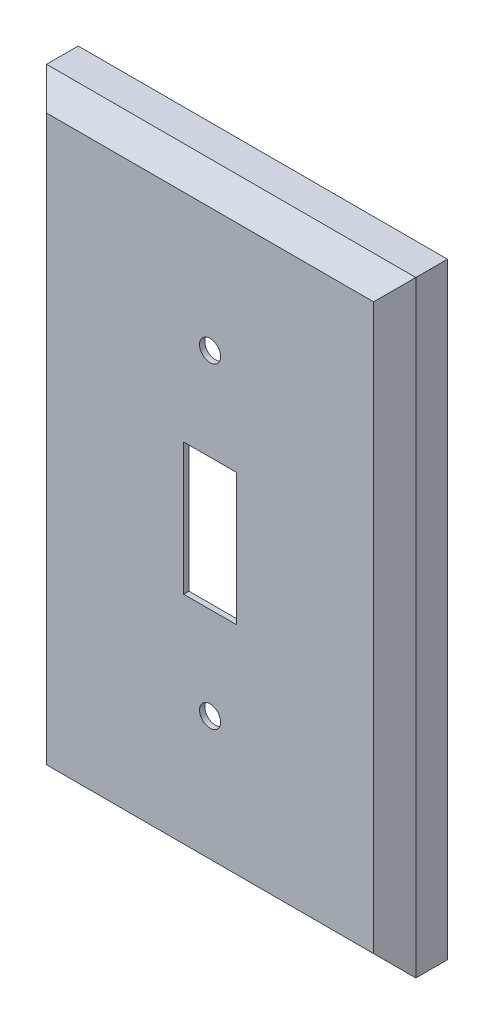
SolidWorks part; units mm, degrees
ref_plane "Přední rovina" through (0, 0, 0) normal (0, 0, 1) x (1, 0, 0)
ref_plane "Horní rovina" through (0, 0, 0) normal (0, 1, 0) x (1, 0, 0)
ref_plane "Pravá rovina" through (0, 0, 0) normal (1, 0, 0) x (0, 0, -1)
sketch "Skica1" plane through (0, 0, 0) normal (0, 0, 1) x (1, 0, 0)
  line L1 (0, 0) -> (70, 0)
  line L2 (0, 0) -> (0, 115)
  line L3 (0, 115) -> (70, 115)
  line L4 (70, 0) -> (70, 115)
  dimension "D1" = 115
  dimension "D2" = 70
extrude "Vysunout1" add sketch "Skica1" along normal blind 10
chamfer "Zkosit1" distance 4 angle 45 4 edges at (35, 115, 10) (70, 57.5, 10) (35, 0, 10) (0, 57.5, 10)
shell "Skořepina1" thickness 1
sketch "Skica3" plane through (0, 0, 10) normal (0, 0, 1) x (1, 0, 0)
  line L0 (35, 111) -> (35, 4) construction
  line L1 (66, 111) -> (4, 111) construction
  line L2 (4, 4) -> (66, 4) construction
  line L3 (4, 57.5) -> (66, 57.5) construction
  line L4 (4, 111) -> (4, 4) construction
  line L5 (66, 4) -> (66, 111) construction
  line L6 (35, 70) -> (35, 45) construction
  line L7 (30, 70) -> (40, 70)
  line L8 (30, 70) -> (30, 45)
  line L9 (30, 45) -> (40, 45)
  line L10 (40, 70) -> (40, 45)
  line L11 (30, 57.5) -> (40, 57.5) construction
  circle A0 centre (35, 87.5) radius 2
  circle A1 centre (35, 27.5) radius 2
  point P20 (35, 57.5)
  point P21 (35, 57.5)
  dimension "D3" = 4
  dimension "D1" = 10
  dimension "D2" = 25
  dimension "D4" = 60
extrude "Odebrat vysunutím1" cut sketch "Skica3" against normal through all
